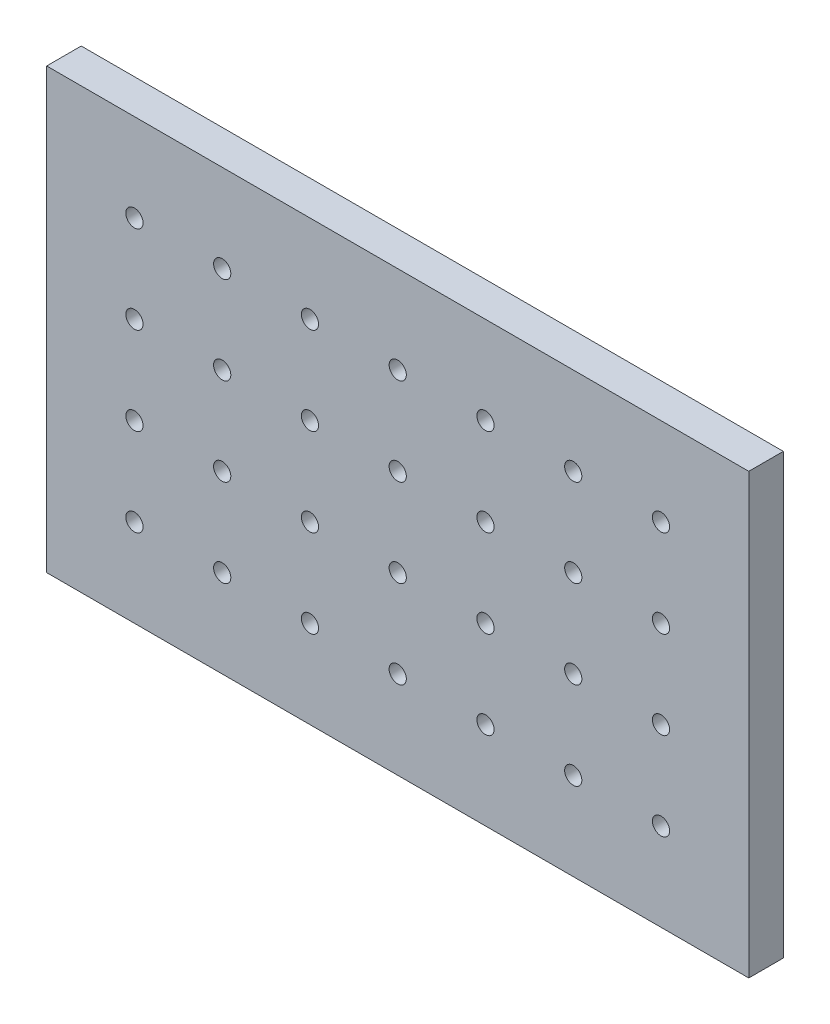
SolidWorks part; units mm, degrees
ref_plane "Front Plane" through (0, 0, 0) normal (0, 0, 1) x (1, 0, 0)
ref_plane "Top Plane" through (0, 0, 0) normal (0, 1, 0) x (1, 0, 0)
ref_plane "Right Plane" through (0, 0, 0) normal (1, 0, 0) x (0, 0, -1)
sketch "Sketch1" plane through (0, 0, 0) normal (0, 0, 1) x (1, 0, 0)
  line L1 (0, 0) -> (-203.2, 0)
  line L2 (0, 0) -> (0, -127)
  line L3 (0, -127) -> (-203.2, -127)
  line L4 (-203.2, 0) -> (-203.2, -127)
  dimension "D1" = 203.2
  dimension "D2" = 127
extrude "Boss-Extrude1" add sketch "Sketch1" along normal blind 10
sketch "Sketch2" plane through (0, 0, 10) normal (0, 0, 1) x (1, 0, 0)
  line L0 (0, 0) -> (-203.2, 0) construction
  line L1 (-203.2, 0) -> (-203.2, -127) construction
  circle A0 centre (-177.8, -25.4) radius 2.49
  circle A1 centre (-152.4, -25.4) radius 2.49
  circle A2 centre (-127, -25.4) radius 2.49
  circle A3 centre (-101.6, -25.4) radius 2.49
  circle A4 centre (-76.2, -25.4) radius 2.49
  circle A5 centre (-50.8, -25.4) radius 2.49
  circle A6 centre (-25.4, -25.4) radius 2.49
  circle A7 centre (-152.4, -50.8) radius 2.49
  circle A8 centre (-127, -50.8) radius 2.49
  circle A9 centre (-101.6, -50.8) radius 2.49
  circle A10 centre (-76.2, -50.8) radius 2.49
  circle A11 centre (-50.8, -50.8) radius 2.49
  circle A12 centre (-25.4, -50.8) radius 2.49
  circle A13 centre (-152.4, -76.2) radius 2.49
  circle A14 centre (-127, -76.2) radius 2.49
  circle A15 centre (-101.6, -76.2) radius 2.49
  circle A16 centre (-76.2, -76.2) radius 2.49
  circle A17 centre (-50.8, -76.2) radius 2.49
  circle A18 centre (-25.4, -76.2) radius 2.49
  circle A19 centre (-152.4, -101.6) radius 2.49
  circle A20 centre (-127, -101.6) radius 2.49
  circle A21 centre (-101.6, -101.6) radius 2.49
  circle A22 centre (-76.2, -101.6) radius 2.49
  circle A23 centre (-50.8, -101.6) radius 2.49
  circle A24 centre (-25.4, -101.6) radius 2.49
  circle A25 centre (-177.8, -50.8) radius 2.49
  circle A26 centre (-177.8, -76.2) radius 2.49
  circle A27 centre (-177.8, -101.6) radius 2.49
  dimension "D1" = 25.4
  dimension "D2" = 25.4
  dimension "D3" = 4.98
  dimension "D4" = 7
  dimension "D5" = 4
extrude "Cut-Extrude1" cut sketch "Sketch2" against normal up to next (10 mm away)
equation "\"inch\"=25.4"
equation "\"D2@Sketch2\"=\"inch\""
equation "\"D1@Sketch2\"=\"inch\""
equation "\"D2@Sketch1\"=\"inch\"*5"
equation "\"D1@Sketch1\"=\"inch\"*8"
